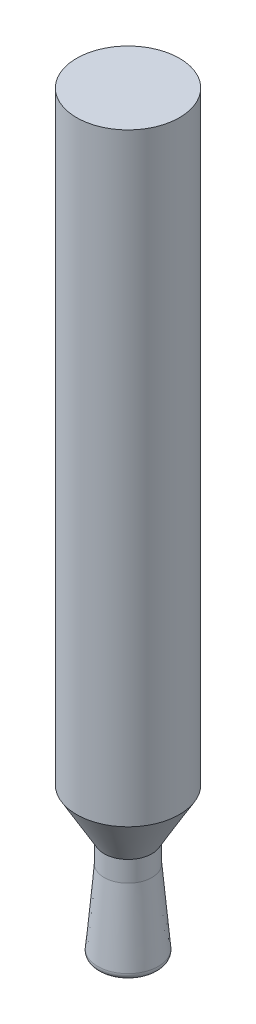
SolidWorks part; units mm, degrees
ref_plane "Vorne" through (0, 0, 0) normal (0, 0, 1) x (1, 0, 0)
ref_plane "Oben" through (0, 0, 0) normal (0, 1, 0) x (1, 0, 0)
ref_plane "Rechts" through (0, 0, 0) normal (1, 0, 0) x (0, 0, -1)
sketch "Sketch1" plane through (0, 0, 0) normal (0, 0, 1) x (1, 0, 0)
  line L0 (0, 0) -> (0, 10) construction
  line L1 (0, 0) -> (1.1972, 0.0903)
  line L2 (1.4735, 0.4156) -> (1.1599, 4)
  line L3 (1.1599, 4) -> (1.1599, 5)
  line L4 (1.1599, 5) -> (2.5, 7.321)
  line L5 (2.5, 7.321) -> (2.5, 36.6565)
  line L6 (2.5, 36.6565) -> (0, 36.6565)
  line L7 (0, 0) -> (0, 36.6565)
  line L8 (0, 0) -> (0, -0.3211) construction
  circle A0 centre (0, 10) radius 10 construction
  arc A1 (1.4735, 0.4156) -> (1.1972, 0.0903) centre (1.1747, 0.3895) cw
  point P13 (1.5, 0.1131)
  dimension "D1" = 20
  dimension "D8" = 0.3
  dimension "D2" = 3
  dimension "D3" = 4
  dimension "D4" = 5
  dimension "D5" = 5
  dimension "D6" = 5
  dimension "D7" = 30
revolve "Revolve3" add sketch "Sketch1" angle 360 about L7
